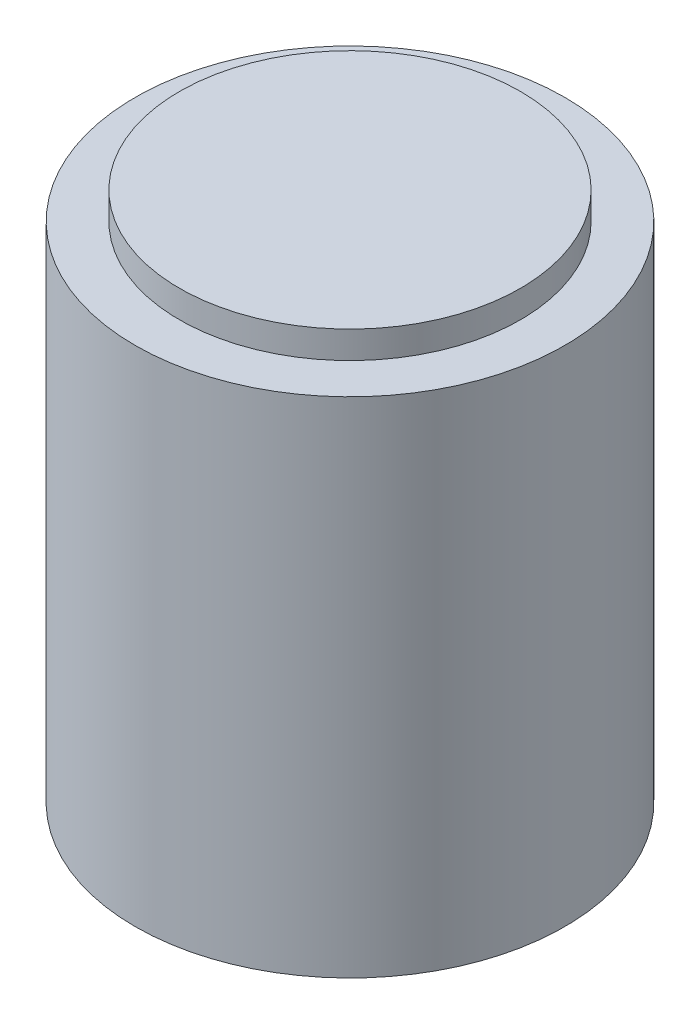
SolidWorks part; units mm, degrees
ref_plane "Front" through (0, 0, 0) normal (0, 0, 1) x (1, 0, 0)
ref_plane "Top" through (0, 0, 0) normal (0, 1, 0) x (1, 0, 0)
ref_plane "Right" through (0, 0, 0) normal (1, 0, 0) x (0, 0, -1)
sketch "Sketch1" plane through (0, 0, 0) normal (0, 0, 1) x (1, 0, 0)
  line L0 (0, 0) -> (0, 38.9) construction
  line L1 (0, 38.9) -> (12.5, 38.9)
  line L2 (12.5, 38.9) -> (12.5, 36.9)
  line L3 (12.5, 36.9) -> (15.75, 36.9)
  line L4 (15.75, 36.9) -> (15.75, 0)
  line L5 (15.75, 0) -> (0, 0)
  line L6 (0, 0) -> (0, 38.9)
  dimension "D1" = 2
  dimension "D2" = 31.5
  dimension "D3" = 36.9
  dimension "D4" = 25
revolve "Revolve1" add sketch "Sketch1" angle 360 about L0
